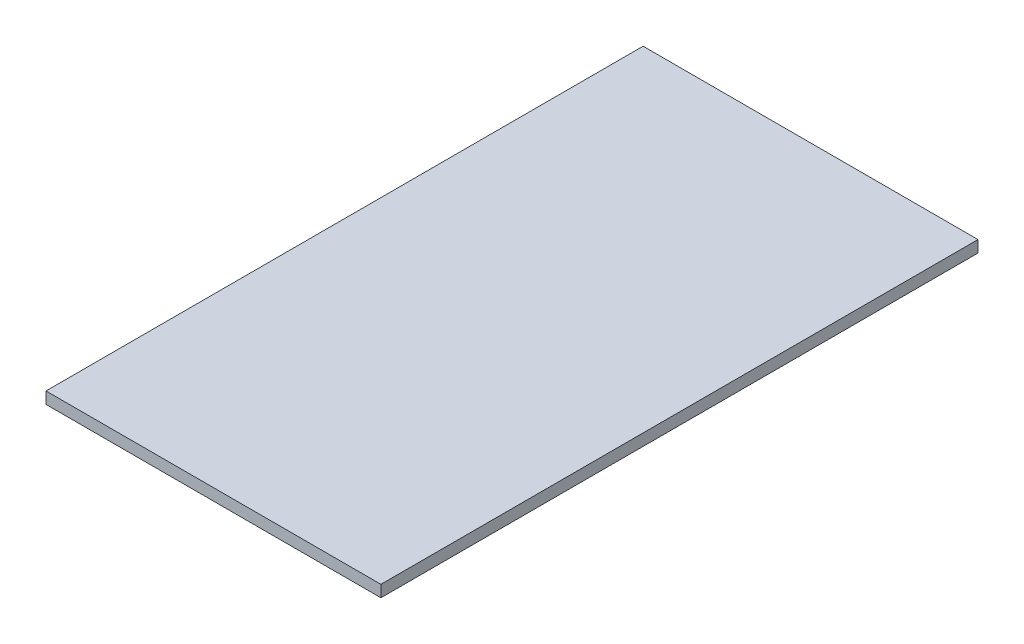
SolidWorks part; units mm, degrees
ref_plane "Спереди" through (0, 0, 0) normal (0, 0, 1) x (1, 0, 0)
ref_plane "Сверху" through (0, 0, 0) normal (0, 1, 0) x (1, 0, 0)
ref_plane "Справа" through (0, 0, 0) normal (1, 0, 0) x (0, 0, -1)
sketch "Эскиз1" plane through (0, 0, 0) normal (0, 1, 0) x (1, 0, 0)
  line L1 (258, -460) -> (-258, -460)
  line L2 (258, -460) -> (258, 460)
  line L3 (258, 460) -> (-258, 460)
  line L4 (-258, -460) -> (-258, 460)
  line L5 (258, -460) -> (-258, 460) construction
  line L6 (258, 460) -> (-258, -460) construction
  point P0 (0, 0)
  dimension "D1" = 516
  dimension "D2" = 920
extrude "Бобышка-Вытянуть1" add sketch "Эскиз1" along normal blind 18
